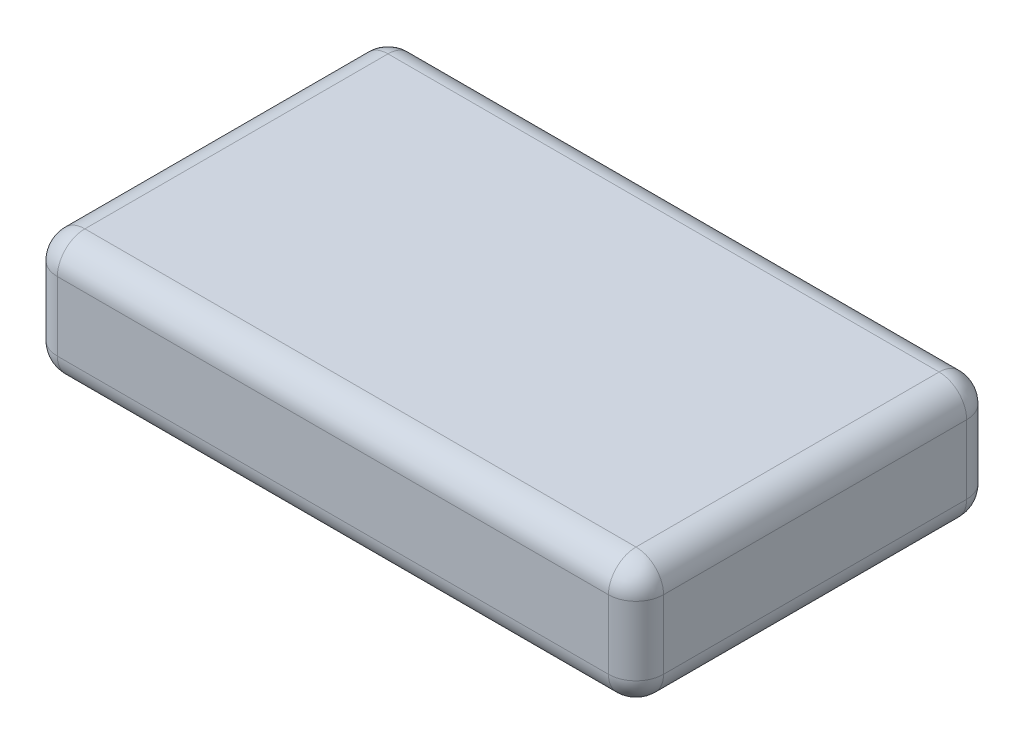
SolidWorks part; units mm, degrees
ref_plane "Piano frontale" through (0, 0, 0) normal (0, 0, 1) x (1, 0, 0)
ref_plane "Piano superiore" through (0, 0, 0) normal (0, 1, 0) x (1, 0, 0)
ref_plane "Piano destro" through (0, 0, 0) normal (1, 0, 0) x (0, 0, -1)
sketch "Schizzo1" plane through (0, 0, 0) normal (0, 1, 0) x (1, 0, 0)
  line L1 (22, 13) -> (-22, 13)
  line L2 (22, 13) -> (22, -13)
  line L3 (22, -13) -> (-22, -13)
  line L4 (-22, 13) -> (-22, -13)
  line L5 (22, 13) -> (-22, -13) construction
  line L6 (22, -13) -> (-22, 13) construction
  point P0 (0, 0)
  dimension "D1" = 44
  dimension "D2" = 26
extrude "Estrusione-Estrusione1" add sketch "Schizzo1" along normal blind 9
fillet "Raccordo1" radius 2 12 edges at (22, 0, 0) (0, 0, 13) (-22, 0, 0) (0, 0, -13) (-22, 4.5, -13) (-22, 4.5, 13) (22, 4.5, 13) (22, 4.5, -13) (22, 9, 0) (0, 9, -13) (-22, 9, 0) (0, 9, 13)
